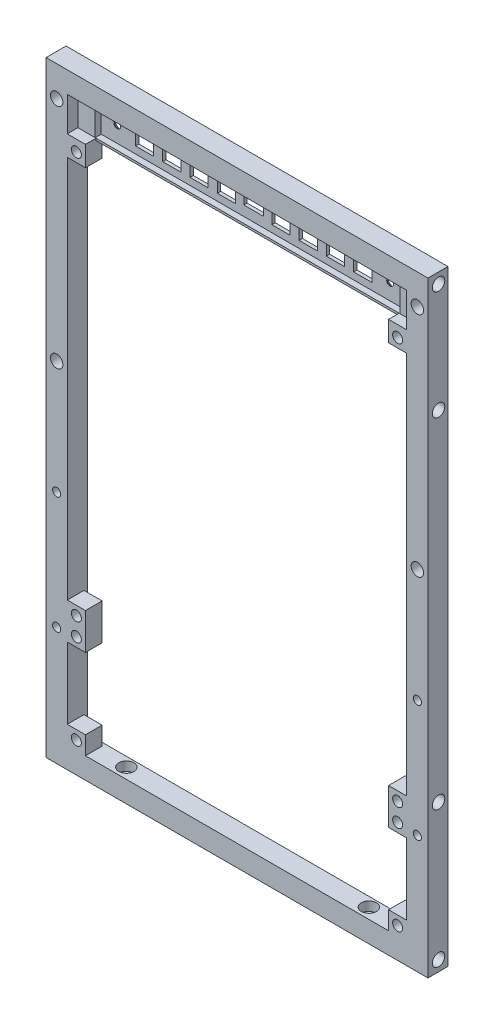
SolidWorks part; units mm, degrees
ref_plane "Front Plane" through (0, 0, 0) normal (0, 0, 1) x (1, 0, 0)
ref_plane "Top Plane" through (0, 0, 0) normal (0, 1, 0) x (1, 0, 0)
ref_plane "Right Plane" through (0, 0, 0) normal (1, 0, 0) x (0, 0, -1)
sketch "Sketch1" plane through (0, 0, 0) normal (0, 0, 1) x (1, 0, 0)
  line L1 (-63, -100) -> (63, -100)
  line L2 (-63, -100) -> (-63, 100)
  line L3 (-63, 100) -> (63, 100)
  line L4 (63, -100) -> (63, 100)
  line L5 (-63, -100) -> (63, 100) construction
  line L6 (-63, 100) -> (63, -100) construction
  line L7 (-56, -93) -> (56, -93)
  line L8 (-56, -93) -> (-56, 93)
  line L9 (-56, 93) -> (56, 93)
  line L10 (56, -93) -> (56, 93)
  line L11 (-56, -93) -> (56, 93) construction
  line L12 (-56, 93) -> (56, -93) construction
  point P0 (0, 0)
  point P6 (0, 0)
  dimension "D1" = 126
  dimension "D2" = 200
  dimension "D3" = 7
  dimension "D4" = 7
extrude "Boss-Extrude1" add sketch "Sketch1" along normal blind 7
sketch "Sketch2" plane through (-63, 0, 0) normal (-1, 0, 0) x (0, 0, 1)
  line L0 (3.5, 96.5) -> (3.5, -96.5) construction
  line L1 (7, 100) -> (0, 100) construction
  circle A0 centre (3.5, -96.5) radius 2.05
  circle A2 centre (3.5, 96.5) radius 2.05
  circle A3 centre (3.5, 60.5) radius 2.05
  circle A4 centre (3.5, -51.5) radius 2.05
  point P2 (3.5, 0)
  point P7 (3.5, 100)
  dimension "D2" = 4.1
  dimension "D3" = 36
  dimension "D4" = 45
  dimension "D1" = 3.5
extrude "Cut-Extrude1" cut sketch "Sketch2" against normal blind 6
mirror "Mirror1" about plane through (0, 0, 0) normal (1, 0, 0) of "Cut-Extrude1"
sketch "Sketch3" plane through (0, -93, 0) normal (0, 1, 0) x (1, 0, 0)
  line L0 (0, 0) -> (0, -7) construction
  line L1 (-56, 0) -> (56, 0) construction
  line L2 (-56, -7) -> (56, -7) construction
  line L3 (40, -3.5) -> (-40, -3.5) construction
  circle A0 centre (40, -3.5) radius 1.35
  circle A1 centre (-40, -3.5) radius 1.35
  point P9 (0, -3.5)
  dimension "D1" = 2.7
  dimension "D2" = 80
extrude "Cut-Extrude2" cut sketch "Sketch3" against normal through all
sketch "Sketch4" plane through (0, -93, 0) normal (0, 1, 0) x (1, 0, 0)
  circle A0 centre (40, -3.5) radius 2.5
  circle A1 centre (-40, -3.5) radius 2.5
  dimension "D1" = 5
extrude "Cut-Extrude3" cut sketch "Sketch4" against normal blind 3
sketch "Sketch5" plane through (0, 0, 0) normal (0, 0, -1) x (-1, 0, 0)
  line L0 (-59.5, -100) -> (-59.5, 100) construction
  line L1 (63, -100) -> (-63, -100) construction
  line L2 (-63, 100) -> (63, 100) construction
  line L3 (-56, 0) -> (-63, 0) construction
  line L4 (-56, -93) -> (-56, 93) construction
  line L5 (-63, -100) -> (-63, 100) construction
  line L6 (0, 100) -> (0, -100) construction
  line L7 (56, -93) -> (-56, -93) construction
  circle A0 centre (-59.5, -22.4) radius 1.35
  circle A1 centre (59.5, -22.4) radius 1.35
  circle A2 centre (-59.5, -61) radius 1.35
  circle A3 centre (59.5, -61) radius 1.35
  point P12 (-59.5, 0)
  point P13 (-59.5, 0)
  dimension "D1" = 2.7
  dimension "D2" = 22.4
  dimension "D3" = 32
extrude "Cut-Extrude4" cut sketch "Sketch5" against normal through all
sketch "Sketch6" plane through (0, 0, 0) normal (0, 0, -1) x (-1, 0, 0)
  circle A0 centre (-59.5, -22.4) radius 2.5
  circle A1 centre (59.5, -22.4) radius 2.5
  circle A2 centre (-59.5, -61) radius 2.5
  circle A3 centre (59.5, -61) radius 2.5
  dimension "D1" = 5
extrude "Cut-Extrude5" cut sketch "Sketch6" against normal blind 3
sketch "Sketch7" plane through (0, 0, 0) normal (0, 0, -1) x (-1, 0, 0)
  line L0 (-56, 93) -> (-63, 93) construction
  line L1 (-63, -100) -> (-63, 100) construction
  line L2 (-59.5, 90) -> (-59.5, 15) construction
  line L3 (-63, 100) -> (63, 100) construction
  circle A0 centre (-59.5, 90) radius 2.05
  circle A1 centre (-59.5, 15) radius 2.05
  point P8 (-59.5, 93)
  dimension "D1" = 4.1
  dimension "D2" = 10
  dimension "D3" = 75
extrude "Cut-Extrude6" cut sketch "Sketch7" against normal through all
mirror "Mirror2" about plane through (0, 0, 0) normal (1, 0, 0) of "Cut-Extrude6"
sketch "Sketch8" plane through (0, 0, 3) normal (0, 0, -1) x (-1, 0, 0)
  line L2 (-60.85, -24.5042) -> (-60.85, -20.2958)
  line L4 (-58.15, -24.5042) -> (-58.15, -20.2958)
  line L5 (-60.85, -24.5042) -> (-58.15, -20.2958) construction
  line L6 (-60.85, -20.2958) -> (-58.15, -24.5042) construction
  line L8 (-60.85, -63.1042) -> (-60.85, -58.8958)
  line L10 (-58.15, -63.1042) -> (-58.15, -58.8958)
  line L11 (-60.85, -63.1042) -> (-58.15, -58.8958) construction
  line L12 (-60.85, -58.8958) -> (-58.15, -63.1042) construction
  circle A0 centre (-59.5, -22.4) radius 2.5 construction
  circle A1 centre (-59.5, -61) radius 2.5 construction
  circle A2 centre (-59.5, -61) radius 2.5 construction
  arc A3 (-58.15, -20.2958) -> (-60.85, -20.2958) centre (-59.5, -22.4) ccw
  arc A4 (-58.15, -58.8958) -> (-60.85, -58.8958) centre (-59.5, -61) ccw
  circle A5 centre (-59.5, -22.4) radius 1.35 construction
  circle A6 centre (-59.5, -61) radius 1.35 construction
  arc A7 (-60.85, -63.1042) -> (-58.15, -63.1042) centre (-59.5, -61) ccw
  arc A8 (-60.85, -24.5042) -> (-58.15, -24.5042) centre (-59.5, -22.4) ccw
  point P0 (-59.5, -22.4)
  point P8 (-59.5, -61)
extrude "Cut-Extrude7" cut sketch "Sketch8" against normal blind 0.2
sketch "Sketch9" plane through (0, 0, 3.2) normal (0, 0, -1) x (-1, 0, 0)
  line L0 (-58.15, -22.4) -> (-58.15, -20.2958) construction
  line L1 (-60.85, -23.75) -> (-58.15, -23.75)
  line L2 (-60.85, -23.75) -> (-60.85, -21.05)
  line L3 (-60.85, -21.05) -> (-58.15, -21.05)
  line L4 (-58.15, -23.75) -> (-58.15, -21.05)
  line L5 (-60.85, -23.75) -> (-58.15, -21.05) construction
  line L6 (-60.85, -21.05) -> (-58.15, -23.75) construction
  line L7 (-58.15, -63.1042) -> (-58.15, -58.8958) construction
  line L8 (-60.85, -62.35) -> (-58.15, -62.35)
  line L9 (-60.85, -62.35) -> (-60.85, -59.65)
  line L10 (-60.85, -59.65) -> (-58.15, -59.65)
  line L11 (-58.15, -62.35) -> (-58.15, -59.65)
  line L12 (-60.85, -62.35) -> (-58.15, -59.65) construction
  line L13 (-60.85, -59.65) -> (-58.15, -62.35) construction
  arc A0 (-58.15, -22.4) -> (-60.85, -22.4) centre (-59.5, -22.4) ccw construction
  point P0 (-59.5, -22.4)
  point P8 (-59.5, -61)
extrude "Cut-Extrude8" cut sketch "Sketch9" against normal blind 0.2
mirror "Mirror3" about plane through (0, 0, 0) normal (1, 0, 0) of "Cut-Extrude8", "Cut-Extrude7"
sketch "Sketch10" plane through (0, 0, 7) normal (0, 0, 1) x (1, 0, 0)
  line L0 (56, -93) -> (56, 93) construction
  line L1 (56, -93) -> (50, -93)
  line L2 (56, -93) -> (56, -87)
  line L3 (56, -87) -> (50, -87)
  line L4 (50, -93) -> (50, -87)
  line L5 (56, -63.5) -> (50, -63.5)
  line L6 (56, -63.5) -> (56, -57.5)
  line L7 (56, -57.5) -> (50, -57.5)
  line L8 (50, -63.5) -> (50, -57.5)
  line L9 (-56, -93) -> (56, -93) construction
  dimension "D1" = 6
  dimension "D2" = 35.5
extrude "Boss-Extrude2" add sketch "Sketch10" against normal offset from surface (5.5 mm away) 1.5 up to face at (-57.45, 15, 0)
sketch "Sketch11" plane through (0, 0, 1.5) normal (0, 0, -1) x (-1, 0, 0)
  line L0 (-56, -63.5) -> (-50, -57.5) construction
  line L2 (-56, -93) -> (-50, -87) construction
  circle A0 centre (-53, -60.5) radius 1.65
  circle A1 centre (-53, -90) radius 1.65
  dimension "D1" = 3.3
extrude "Cut-Extrude9" cut sketch "Sketch11" against normal through all
mirror "Mirror4" about plane through (0, 0, 0) normal (1, 0, 0) of "Cut-Extrude9", "Boss-Extrude2"
sketch "Sketch12" plane through (0, 0, 0) normal (0, 0, -1) x (-1, 0, 0)
  line L0 (56, 93) -> (56, -93) construction
  line L1 (-56, 93) -> (56, 93)
  line L2 (-56, 93) -> (-56, 81)
  line L3 (-56, 81) -> (56, 81)
  line L4 (56, 93) -> (56, 81)
  dimension "D1" = 12
extrude "Boss-Extrude3" add sketch "Sketch12" against normal blind 1.5
sketch "Sketch13" plane through (0, 0, 1.5) normal (0, 0, 1) x (1, 0, 0)
  line L0 (-56, 93) -> (56, 81) construction
  line L2 (-50.3, 81.7) -> (50.3, 81.7)
  line L3 (-50.3, 81.7) -> (-50.3, 92.3)
  line L4 (-50.3, 92.3) -> (50.3, 92.3)
  line L5 (50.3, 81.7) -> (50.3, 92.3)
  line L6 (-50.3, 81.7) -> (50.3, 92.3) construction
  line L7 (-50.3, 92.3) -> (50.3, 81.7) construction
  line L8 (-56, 81) -> (56, 81)
  line L9 (-56, 81) -> (-56, 93)
  line L10 (-56, 93) -> (56, 93)
  line L11 (56, 81) -> (56, 93)
  line L12 (-56, 81) -> (56, 93) construction
  line L13 (-56, 93) -> (56, 81) construction
  point P4 (0, 87)
  point P9 (0, 87)
  dimension "D1" = 100.6
  dimension "D2" = 10.6
extrude "Boss-Extrude4" add sketch "Sketch13" along normal blind 2
sketch "Sketch14" plane through (0, 0, 1.5) normal (0, 0, 1) x (1, 0, 0)
  line L0 (0, 92.3) -> (0, 81.7) construction
  line L1 (50.3, 92.3) -> (-50.3, 92.3) construction
  line L2 (-50.3, 81.7) -> (50.3, 81.7) construction
  line L3 (-50.3, 87) -> (50.3, 87) construction
  line L4 (50.3, 81.7) -> (50.3, 92.3) construction
  line L5 (-33, 90) -> (-39, 90)
  line L6 (-3.25, 85) -> (3.25, 85)
  line L7 (-3.25, 85) -> (-3.25, 89)
  line L8 (-3.25, 89) -> (3.25, 89)
  line L9 (3.25, 85) -> (3.25, 89)
  line L10 (-3.25, 85) -> (3.25, 89) construction
  line L11 (-3.25, 89) -> (3.25, 85) construction
  line L12 (6, 84) -> (12, 84)
  line L13 (6, 84) -> (6, 90)
  line L14 (6, 90) -> (12, 90)
  line L15 (12, 84) -> (12, 90)
  line L16 (6, 84) -> (12, 90) construction
  line L17 (6, 90) -> (12, 84) construction
  line L18 (15, 84) -> (21, 84)
  line L19 (15, 84) -> (15, 90)
  line L20 (15, 90) -> (21, 90)
  line L21 (21, 84) -> (21, 90)
  line L22 (15, 84) -> (21, 90) construction
  line L23 (15, 90) -> (21, 84) construction
  line L24 (24, 84) -> (30, 84)
  line L25 (24, 84) -> (24, 90)
  line L26 (24, 90) -> (30, 90)
  line L27 (30, 84) -> (30, 90)
  line L28 (24, 84) -> (30, 90) construction
  line L29 (24, 90) -> (30, 84) construction
  line L30 (33, 84) -> (39, 84)
  line L31 (33, 84) -> (33, 90)
  line L32 (33, 90) -> (39, 90)
  line L33 (39, 84) -> (39, 90)
  line L34 (33, 84) -> (39, 90) construction
  line L35 (33, 90) -> (39, 84) construction
  line L36 (-39, 84) -> (-39, 90)
  line L37 (-33, 84) -> (-39, 84)
  line L38 (-33, 84) -> (-33, 90)
  line L39 (-24, 90) -> (-30, 90)
  line L40 (-30, 84) -> (-30, 90)
  line L41 (-24, 84) -> (-30, 84)
  line L42 (-24, 84) -> (-24, 90)
  line L43 (-15, 90) -> (-21, 90)
  line L44 (-21, 84) -> (-21, 90)
  line L45 (-15, 84) -> (-21, 84)
  line L46 (-15, 84) -> (-15, 90)
  line L47 (-6, 90) -> (-12, 90)
  line L48 (-12, 84) -> (-12, 90)
  line L49 (-6, 84) -> (-12, 84)
  line L50 (-6, 84) -> (-6, 90)
  circle A0 centre (-45, 87) radius 1.3 construction
  circle A1 centre (45, 87) radius 1.3 construction
  point P6 (0, 87)
  point P11 (0, 87)
  point P16 (9, 87)
  point P21 (18, 87)
  point P26 (27, 87)
  point P31 (36, 87)
  dimension "D10" = 2.6
  dimension "D9" = 45
  dimension "D1" = 6.5
  dimension "D2" = 4
  dimension "D3" = 6
  dimension "D4" = 9
  dimension "D5" = 9
  dimension "D6" = 9
  dimension "D7" = 9
  dimension "D8" = 45
extrude "Cut-Extrude10" cut sketch "Sketch14" against normal through all
sketch "Sketch15" plane through (0, 0, 1.5) normal (0, 0, 1) x (1, 0, 0)
  circle A0 centre (-45, 87) radius 1
  circle A1 centre (45, 87) radius 1
  dimension "D1" = 2
extrude "Boss-Extrude5" add sketch "Sketch15" along normal up to surface (2 mm away) up to face at (0, 87, 3.5)
chamfer "Chamfer1" distance 0.4 angle 45 4 edges at (-56, -6, 0) (56, -6, 0) (0, -93, 0) (0, 81, 0)
chamfer "Chamfer2" distance 0.4 angle 45 4 edges at (0, 100, 0) (-63, 0, 0) (0, -100, 0) (63, 0, 0)
chamfer "Chamfer3" distance 0.4 angle 45 36 edges at (-36, 84, 0) (-39, 87, 0) (-36, 90, 0) (-33, 87, 0) (-27, 84, 0) (-30, 87, 0) (-27, 90, 0) (-24, 87, 0) (-18, 84, 0) (-21, 87, 0) (-18, 90, 0) (-15, 87, 0) (-9, 84, 0) (-12, 87, 0) (-9, 90, 0) (-6, 87, 0) (0, 85, 0) (-3.25, 87, 0) (0, 89, 0) (3.25, 87, 0) (9, 84, 0) (6, 87, 0) (9, 90, 0) (12, 87, 0) (18, 84, 0) (15, 87, 0) (18, 90, 0) (21, 87, 0) (36, 84, 0) (33, 87, 0) (36, 90, 0) (39, 87, 0) (27, 84, 0) (24, 87, 0) (27, 90, 0) (30, 87, 0)
sketch "Sketch16" plane through (0, 0, 7) normal (0, 0, 1) x (1, 0, 0)
  line L0 (-50, 81) -> (-50, 81.7)
  line L1 (-56, -57.5) -> (-50, -57.5)
  line L2 (-56, -57.5) -> (-56, -51.5)
  line L3 (-56, -51.5) -> (-50, -51.5)
  line L4 (-50, -57.5) -> (-50, -51.5)
  line L5 (56, -57.5) -> (50, -57.5)
  line L6 (56, -57.5) -> (56, -51.5)
  line L7 (56, -51.5) -> (50, -51.5)
  line L8 (50, -57.5) -> (50, -51.5)
  line L9 (56, 81) -> (50, 81) construction
  line L10 (56, 81) -> (56, 75)
  line L11 (56, 75) -> (50, 75)
  line L12 (50, 81) -> (50, 75)
  line L13 (-56, 81) -> (-50, 81) construction
  line L14 (-56, 81) -> (-56, 75)
  line L15 (-56, 75) -> (-50, 75)
  line L16 (-50, 81) -> (-50, 75)
  line L17 (-50.3, 81.7) -> (50.3, 81.7) construction
  line L18 (-50, 81.7) -> (-56, 81.7)
  line L19 (-56, 93) -> (-56, 81) construction
  line L20 (-56, 81.7) -> (-56, 81)
  line L21 (50, 81) -> (50, 81.7)
  line L22 (50, 81.7) -> (56, 81.7)
  line L23 (56, 81) -> (56, 93) construction
  line L24 (56, 81.7) -> (56, 81)
  dimension "D1" = 6
extrude "Boss-Extrude7" add sketch "Sketch16" against normal offset from surface (5.5 mm away) 1.5 up to face at (-36, 87, 0)
sketch "Sketch17" plane through (0, 0, 1.5) normal (0, 0, -1) x (-1, 0, 0)
  line L0 (-50, 75) -> (50, -51.5) construction
  line L1 (-50, -51.5) -> (-50, -63.5) construction
  line L2 (-53, -54.5) -> (53, -54.5) construction
  line L3 (-53, -54.5) -> (-53, 78) construction
  line L4 (-53, 78) -> (53, 78) construction
  line L5 (53, -54.5) -> (53, 78) construction
  line L6 (-53, -54.5) -> (53, 78) construction
  line L7 (-53, 78) -> (53, -54.5) construction
  line L8 (50, -51.5) -> (56, -51.5) construction
  circle A0 centre (-53, -54.5) radius 1.65
  circle A1 centre (53, -54.5) radius 1.65
  circle A2 centre (53, 78) radius 1.65
  circle A3 centre (-53, 78) radius 1.65
  point P4 (0, 11.75)
  dimension "D3" = 3.3
  dimension "D1" = 3
  dimension "D2" = 3
extrude "Cut-Extrude11" cut sketch "Sketch17" against normal through all
sketch "Sketch18" plane through (0, 0, 1.5) normal (0, 0, 1) x (1, 0, 0)
  circle A0 centre (-45, 87) radius 1.1
  circle A1 centre (45, 87) radius 1.1
  dimension "D1" = 2.2
extrude "Cut-Extrude12" cut sketch "Sketch18" against normal through all both and the other way through all
chamfer "Chamfer4" distance 1.3 angle 45 2 edges at (-43.9, 87, 0) (46.1, 87, 0)
